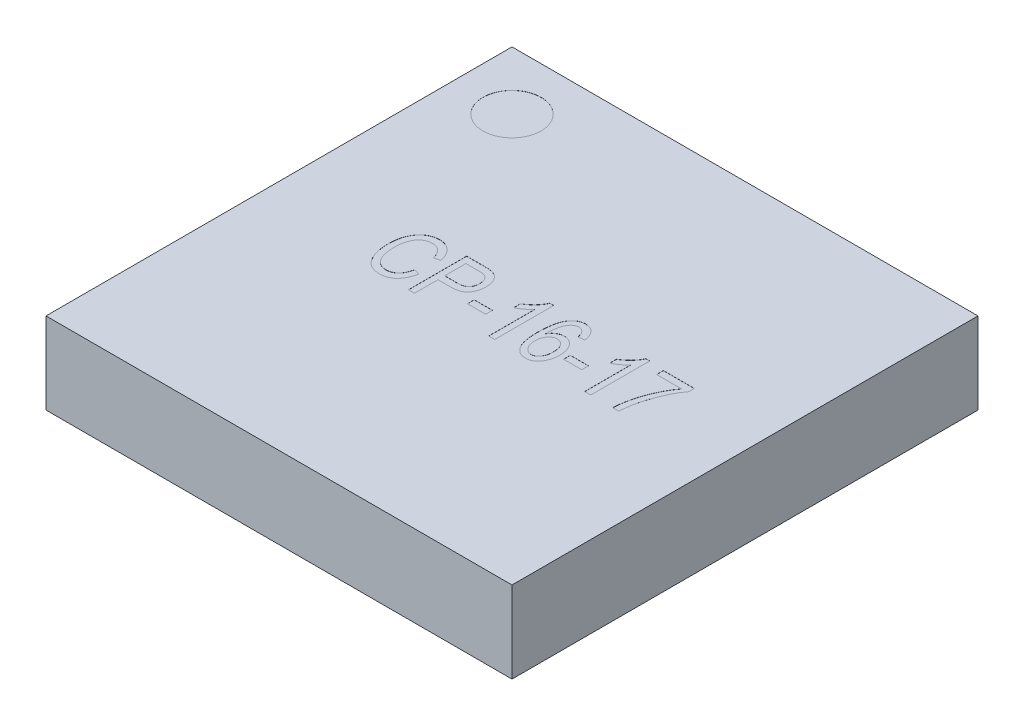
SolidWorks part; units mm, degrees
ref_plane "Front Plane" through (0, 0, 0) normal (0, 0, 1) x (1, 0, 0)
ref_plane "Top Plane" through (0, 0, 0) normal (0, 1, 0) x (1, 0, 0)
ref_plane "Right Plane" through (0, 0, 0) normal (1, 0, 0) x (0, 0, -1)
sketch "Sketch1" plane through (0, 0, 0) normal (0, 1, 0) x (1, 0, 0)
  line L1 (-2, -2) -> (2, -2)
  line L2 (-2, -2) -> (-2, 2)
  line L3 (-2, 2) -> (2, 2)
  line L4 (2, -2) -> (2, 2)
  line L5 (-2, -2) -> (2, 2) construction
  line L6 (-2, 2) -> (2, -2) construction
  point P0 (0, 0)
  dimension "D1" = 4
extrude "Boss-Extrude1" add sketch "Sketch1" along normal blind 0.7
sketch "Sketch2" plane through (0, 0.7, 0) normal (0, 1, 0) x (1, 0, 0)
  line L0 (2, 2) -> (-2, 2) construction
  line L1 (-2, 2) -> (-2, -2) construction
  circle A0 centre (-1.5, 1.5) radius 0.25
  dimension "D1" = 0.5
  dimension "D2" = 0.5
  dimension "D3" = 0.5
extrude "Cut-Extrude1" cut sketch "Sketch2" against normal blind 0.001
sketch "Sketch3" plane through (0, 0.7, 0) normal (0, 1, 0) x (1, 0, 0)
  line L0 (-1.1, -0.25) -> (1.1, -0.25) construction
  line L1 (0, -0.385) -> (0, 0.385) construction
  line L2 (-0.385, 0) -> (0.385, 0) construction
  text T0 "CP-16-17" font "Arial Narrow" height 0.5
  point P2 (0, -0.25)
  dimension "D1" = 2.2
  dimension "D2" = 0.25
extrude "Cut-Extrude2" cut sketch "Sketch3" against normal blind 0.001
